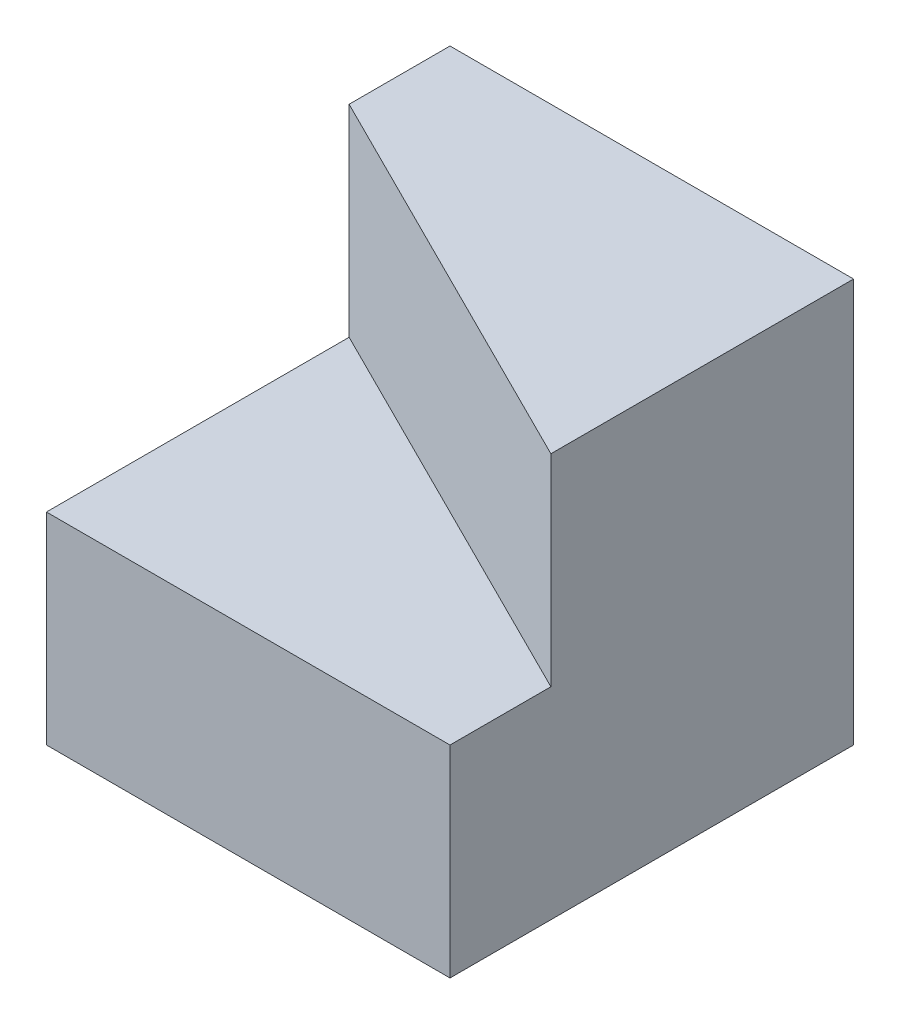
SolidWorks part; units mm, degrees
ref_plane "Front Plane" through (0, 0, 0) normal (0, 0, 1) x (1, 0, 0)
ref_plane "Top Plane" through (0, 0, 0) normal (0, 1, 0) x (1, 0, 0)
ref_plane "Right Plane" through (0, 0, 0) normal (1, 0, 0) x (0, 0, -1)
sketch "Sketch1" plane through (0, 0, 0) normal (0, 0, 1) x (1, 0, 0)
  line L1 (0, 0) -> (40, 0)
  line L2 (0, 0) -> (0, 40)
  line L3 (0, 40) -> (40, 40)
  line L4 (40, 0) -> (40, 40)
  dimension "D1" = 40
  dimension "D2" = 40
extrude "Boss-Extrude1" add sketch "Sketch1" along normal blind 40
sketch "Sketch3" plane through (0, 40, 0) normal (0, 1, 0) x (1, 0, 0)
  line L0 (0, -10) -> (40, -30)
  line L1 (0, -40) -> (0, 0) construction
  line L2 (40, -40) -> (40, 0) construction
  line L3 (40, -30) -> (40, -40)
  line L4 (40, -40) -> (0, -40)
  line L5 (0, -40) -> (0, -10)
  dimension "D1" = 30
  dimension "D2" = 10
extrude "Cut-Extrude1" cut sketch "Sketch3" against normal blind 20
